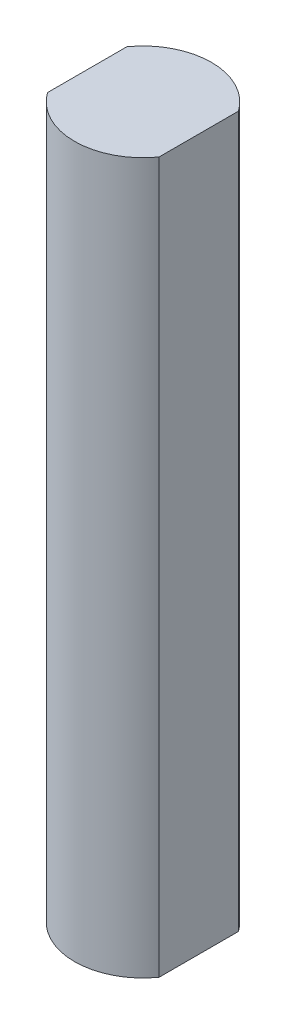
SolidWorks part; units mm, degrees
ref_plane "Front Plane" through (0, 0, 0) normal (0, 0, 1) x (1, 0, 0)
ref_plane "Top Plane" through (0, 0, 0) normal (0, 1, 0) x (1, 0, 0)
ref_plane "Right Plane" through (0, 0, 0) normal (1, 0, 0) x (0, 0, -1)
sketch "Sketch1" plane through (0, 0, 0) normal (0, 1, 0) x (1, 0, 0)
  circle A0 centre (0, 0) radius 4.3815
  dimension "D1" = 8.763
extrude "Boss-Extrude1" add sketch "Sketch1" along normal blind 45.466
sketch "Sketch2" plane through (0, 45.466, 0) normal (0, 1, 0) x (1, 0, 0)
  line L0 (3.5701, 2.54) -> (3.5701, -2.54)
  line L1 (-3.5701, 2.54) -> (-3.5701, -2.54)
  circle A0 centre (0, 0) radius 4.3815 construction
  circle M3 centre (0, 0) radius 4.3815
  dimension "D1" = 5.08
  dimension "D2" = 5.08
extrude "Cut-Extrude1" cut sketch "Sketch2" against normal blind 48.26 contours L1 M3 | L0 M3
